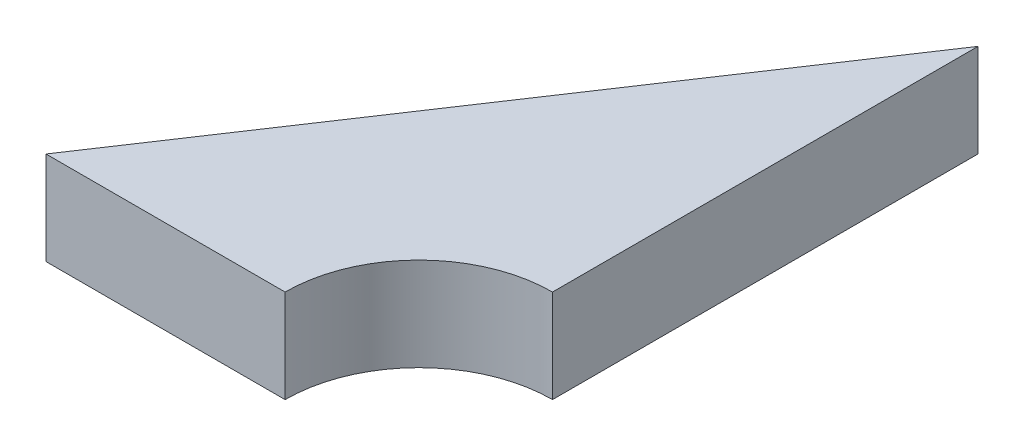
SolidWorks part; units mm, degrees
ref_plane "Front Plane" through (0, 0, 0) normal (0, 0, 1) x (1, 0, 0)
ref_plane "Top Plane" through (0, 0, 0) normal (0, 1, 0) x (1, 0, 0)
ref_plane "Right Plane" through (0, 0, 0) normal (1, 0, 0) x (0, 0, -1)
sketch "Sketch1" plane through (0, 0, 0) normal (0, 1, 0) x (1, 0, 0)
  line L0 (-10.197, -4.1569) -> (2.6293, -4.1569)
  line L1 (9.803, 3.0169) -> (9.803, 25.8431)
  line L2 (9.803, 25.8431) -> (-10.197, -4.1569)
  arc A0 (9.803, 3.0169) -> (2.6293, -4.1569) centre (9.803, -4.1569) ccw
  dimension "D1" = 20
  dimension "D2" = 30
extrude "Boss-Extrude1" add sketch "Sketch1" along normal blind 5
